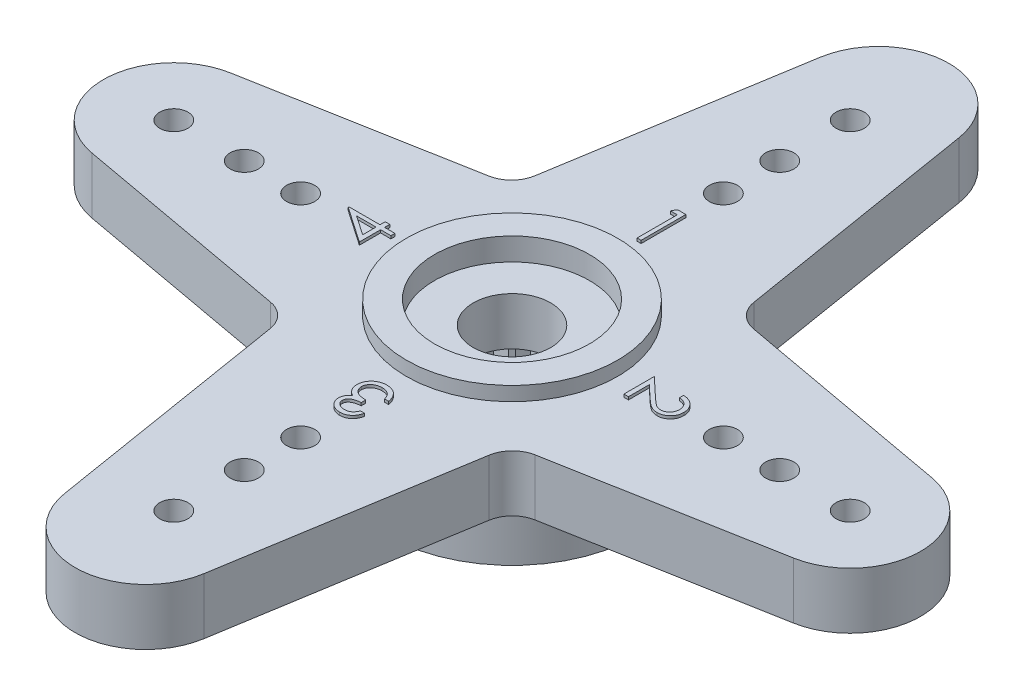
SolidWorks part; units mm, degrees
material "Nylon 101"
ref_plane "Front Plane" through (0, 0, 0) normal (0, 0, 1) x (1, 0, 0)
ref_plane "Top Plane" through (0, 0, 0) normal (0, 1, 0) x (1, 0, 0)
ref_plane "Right Plane" through (0, 0, 0) normal (1, 0, 0) x (0, 0, -1)
sketch "Sketch1" plane through (0, 0, 0) normal (0, 1, 0) x (1, 0, 0)
  line L0 (0, 15.5) -> (0, -15.5) construction
  line L1 (-15.5, 0) -> (15.5, 0) construction
  line L2 (-2.4674, 13.4022) -> (-4, 4) construction
  line L3 (4, -4) -> (-4, -4) construction
  line L4 (4, -4) -> (4, 4) construction
  line L5 (4, 4) -> (-4, 4) construction
  line L6 (-4, -4) -> (-4, 4) construction
  line L7 (4, -4) -> (-4, 4) construction
  line L8 (4, 4) -> (-4, -4) construction
  line L9 (-4, 4) -> (-2.4674, 13.4022)
  line L10 (4, 4) -> (2.4674, 13.4022)
  line L11 (4, -4) -> (2.4674, -13.4022)
  line L12 (-4, -4) -> (-2.4674, -13.4022)
  line L13 (-4, 4) -> (-12.5927, 2.4331) construction
  line L14 (-4, 4) -> (-12.4485, 2.4594)
  line L15 (-4, -4) -> (-12.4485, -2.4594)
  line L16 (4, -4) -> (12.4485, -2.4594)
  line L17 (4, 4) -> (12.4485, 2.4594)
  circle A0 centre (0, 0) radius 15.5 construction
  circle A1 centre (0, 0) radius 14.5 construction
  arc A2 (2.4674, 13.4022) -> (-2.4674, 13.4022) centre (0, 13) ccw
  arc A3 (2.4674, -13.4022) -> (-2.4674, -13.4022) centre (0, -13) cw
  arc A4 (-12.4485, 2.4594) -> (-12.4485, -2.4594) centre (-12, 0) ccw
  arc A5 (12.4485, 2.4594) -> (12.4485, -2.4594) centre (12, 0) cw
  circle A6 centre (0, 0) radius 12 construction
  circle A7 centre (0, 0) radius 9.5 construction
  circle A8 centre (0, 0) radius 7.5 construction
  circle A9 centre (0, 12) radius 0.5
  circle A10 centre (0, 9.5) radius 0.5
  circle A11 centre (0, 7.5) radius 0.5
  circle A12 centre (12, 0) radius 0.5
  circle A13 centre (9.5, 0) radius 0.5
  circle A14 centre (7.5, 0) radius 0.5
  circle A15 centre (0, -12) radius 0.5
  circle A16 centre (0, -9.5) radius 0.5
  circle A17 centre (0, -7.5) radius 0.5
  circle A18 centre (-12, 0) radius 0.5
  circle A19 centre (-9.5, 0) radius 0.5
  circle A20 centre (-7.5, 0) radius 0.5
  circle A21 centre (0, 0) radius 1.375
  point P59 (0, 0)
  dimension "D1" = 31
  dimension "D2" = 1
  dimension "D3" = 5
  dimension "D4" = 5
  dimension "D5" = 8
  dimension "D6" = 8
  dimension "D7" = 15
  dimension "D9" = 24
  dimension "D11" = 1
  dimension "D12" = 1
  dimension "D13" = 4
  dimension "D8" = 19
  dimension "D10" = 1
  dimension "D14" = 2.75
extrude "Boss-Extrude1" add sketch "Sketch1" along normal blind 2
sketch "Sketch2" plane through (0, 2, 0) normal (0, 1, 0) x (1, 0, 0)
  circle A0 centre (0, 0) radius 3.75
  circle A1 centre (0, 0) radius 2.75
  dimension "D1" = 7.5
  dimension "D2" = 1
extrude "Boss-Extrude2" add sketch "Sketch2" along normal blind 0.5
sketch "Sketch3" plane through (0, 2.5, 0) normal (0, 1, 0) x (1, 0, 0)
  circle A2 centre (0, 0) radius 1.375
  circle A3 centre (0, 0) radius 2.75
  circle A5 centre (0, 0) radius 2.75
  circle A6 centre (0, 0) radius 2.75
  circle M6 centre (0, 0) radius 2.75
  dimension "D1" = 0
extrude "Cut-Extrude1" cut sketch "Sketch3" against normal blind 0.8 contours A2 M6
sketch "Sketch4" plane through (0, 0, 0) normal (0, -1, 0) x (1, 0, 0)
  circle A0 centre (0, 0) radius 4.5
  circle A1 centre (0, 0) radius 2.5
  dimension "D1" = 9
  dimension "D2" = 2
extrude "Boss-Extrude3" add sketch "Sketch4" along normal blind 2.5
sketch "Sketch5" plane through (0, -2.5, 0) normal (0, -1, 0) x (1, 0, 0)
  line L0 (0, 0) -> (0, 0.6245) construction
  line L1 (0, 3) -> (-0.299, 2.4821)
  line L2 (0, 3) -> (0.299, 2.4821)
  line L3 (0.9271, 2.8532) -> (0.4826, 2.453)
  line L4 (0.9271, 2.8532) -> (1.0514, 2.2682)
  line L5 (1.7634, 2.4271) -> (1.217, 2.1838)
  line L6 (1.7634, 2.4271) -> (1.7008, 1.8323)
  line L7 (2.4271, 1.7634) -> (1.8323, 1.7008)
  line L8 (2.4271, 1.7634) -> (2.1838, 1.217)
  line L9 (2.8532, 0.9271) -> (2.2682, 1.0514)
  line L10 (2.8532, 0.9271) -> (2.453, 0.4826)
  line L11 (3, 0) -> (2.4821, 0.299)
  line L12 (3, 0) -> (2.4821, -0.299)
  line L13 (2.8532, -0.9271) -> (2.453, -0.4826)
  line L14 (2.8532, -0.9271) -> (2.2682, -1.0514)
  line L15 (2.4271, -1.7634) -> (2.1838, -1.217)
  line L16 (2.4271, -1.7634) -> (1.8323, -1.7008)
  line L17 (1.7634, -2.4271) -> (1.7008, -1.8323)
  line L18 (1.7634, -2.4271) -> (1.217, -2.1838)
  line L19 (0.9271, -2.8532) -> (1.0514, -2.2682)
  line L20 (0.9271, -2.8532) -> (0.4826, -2.453)
  line L21 (0, -3) -> (0.299, -2.4821)
  line L22 (0, -3) -> (-0.299, -2.4821)
  line L23 (-0.9271, -2.8532) -> (-0.4826, -2.453)
  line L24 (-0.9271, -2.8532) -> (-1.0514, -2.2682)
  line L25 (-1.7634, -2.4271) -> (-1.217, -2.1838)
  line L26 (-1.7634, -2.4271) -> (-1.7008, -1.8323)
  line L27 (-2.4271, -1.7634) -> (-1.8323, -1.7008)
  line L28 (-2.4271, -1.7634) -> (-2.1838, -1.217)
  line L29 (-2.8532, -0.9271) -> (-2.2682, -1.0514)
  line L30 (-2.8532, -0.9271) -> (-2.453, -0.4826)
  line L31 (-3, 0) -> (-2.4821, -0.299)
  line L32 (-3, 0) -> (-2.4821, 0.299)
  line L33 (-2.8532, 0.9271) -> (-2.453, 0.4826)
  line L34 (-2.8532, 0.9271) -> (-2.2682, 1.0514)
  line L35 (-2.4271, 1.7634) -> (-2.1838, 1.217)
  line L36 (-2.4271, 1.7634) -> (-1.8323, 1.7008)
  line L37 (-1.7634, 2.4271) -> (-1.7008, 1.8323)
  line L38 (-1.7634, 2.4271) -> (-1.217, 2.1838)
  line L39 (-0.9271, 2.8532) -> (-1.0514, 2.2682)
  line L40 (-0.9271, 2.8532) -> (-0.4826, 2.453)
  circle A0 centre (0, 0) radius 2.5 construction
  arc A1 (-2.1838, 1.217) -> (-2.2682, 1.0514) centre (0, 0) ccw
  arc A2 (-1.7008, 1.8323) -> (-1.8323, 1.7008) centre (0, 0) ccw
  arc A3 (-1.0514, 2.2682) -> (-1.217, 2.1838) centre (0, 0) ccw
  arc A4 (-0.299, 2.4821) -> (-0.4826, 2.453) centre (0, 0) ccw
  arc A5 (0.4826, 2.453) -> (0.299, 2.4821) centre (0, 0) ccw
  arc A6 (1.217, 2.1838) -> (1.0514, 2.2682) centre (0, 0) ccw
  arc A7 (1.8323, 1.7008) -> (1.7008, 1.8323) centre (0, 0) ccw
  arc A8 (2.2682, 1.0514) -> (2.1838, 1.217) centre (0, 0) ccw
  arc A9 (2.4821, 0.299) -> (2.453, 0.4826) centre (0, 0) ccw
  arc A10 (2.453, -0.4826) -> (2.4821, -0.299) centre (0, 0) ccw
  arc A11 (2.1838, -1.217) -> (2.2682, -1.0514) centre (0, 0) ccw
  arc A12 (1.7008, -1.8323) -> (1.8323, -1.7008) centre (0, 0) ccw
  arc A13 (1.0514, -2.2682) -> (1.217, -2.1838) centre (0, 0) ccw
  arc A14 (0.299, -2.4821) -> (0.4826, -2.453) centre (0, 0) ccw
  arc A15 (-0.4826, -2.453) -> (0, -2.5) centre (0, 0) ccw
  arc A16 (-1.217, -2.1838) -> (-1.0514, -2.2682) centre (0, 0) ccw
  arc A17 (-1.8323, -1.7008) -> (-1.7008, -1.8323) centre (0, 0) ccw
  arc A18 (-2.2682, -1.0514) -> (-2.1838, -1.217) centre (0, 0) ccw
  arc A19 (-2.4821, -0.299) -> (-2.453, -0.4826) centre (0, 0) ccw
  arc A20 (-2.453, 0.4826) -> (-2.4821, 0.299) centre (0, 0) ccw
  point P68 (0, 0)
  circle M5 centre (0, 0) radius 2.5
  dimension "D1" = 30
  dimension "D2" = 3
  dimension "D3" = 20
extrude "Cut-Extrude3" cut sketch "Sketch5" against normal up to surface (2.5 mm away) contours L36 L35 M5 | L34 L33 M5 | L32 L31 M5 | L30 L29 M5 | L28 L27 M5 | L26 L25 M5 | L24 L23 M5 | L0 L21 M5 | L22 L0 M5 | L20 L19 M5 | L18 L17 M5 | L16 L15 M5 | L14 L13 M5 | L12 L11 M5 | L10 L9 M5 | L8 L7 M5 | L6 L5 M5 | L4 L3 M5 | L0 L2 M5 | L0 L1 M5 | L40 L39 M5 | L38 L37 M5
sketch "Sketch6" plane through (0, 2, 0) normal (0, 1, 0) x (1, 0, 0)
  line L1 (4.5, -4.5) -> (-4.5, -4.5) construction
  line L2 (4.5, -4.5) -> (4.5, 4.5) construction
  line L3 (4.5, 4.5) -> (-4.5, 4.5) construction
  line L4 (-4.5, -4.5) -> (-4.5, 4.5) construction
  line L5 (4.5, -4.5) -> (-4.5, 4.5) construction
  line L6 (4.5, 4.5) -> (-4.5, -4.5) construction
  circle A0 centre (0, 0) radius 4.5 construction
  text T0 "1" font "Century Gothic" height in points 6
  text T1 "2" font "Century Gothic" height in points 6
  text T2 "3" font "Century Gothic" height in points 6
  text T3 "4" font "Century Gothic" height in points 6
  dimension "D1" = 9
  dimension "D2" = 9
  dimension "D3" = 9
extrude "Boss-Extrude4" add sketch "Sketch6" along normal blind 0.1
fillet "Fillet1" radius 1 4 edges at (-4, 1, -4) (-4, 1, 4) (4, 1, 4) (4, 1, -4)
